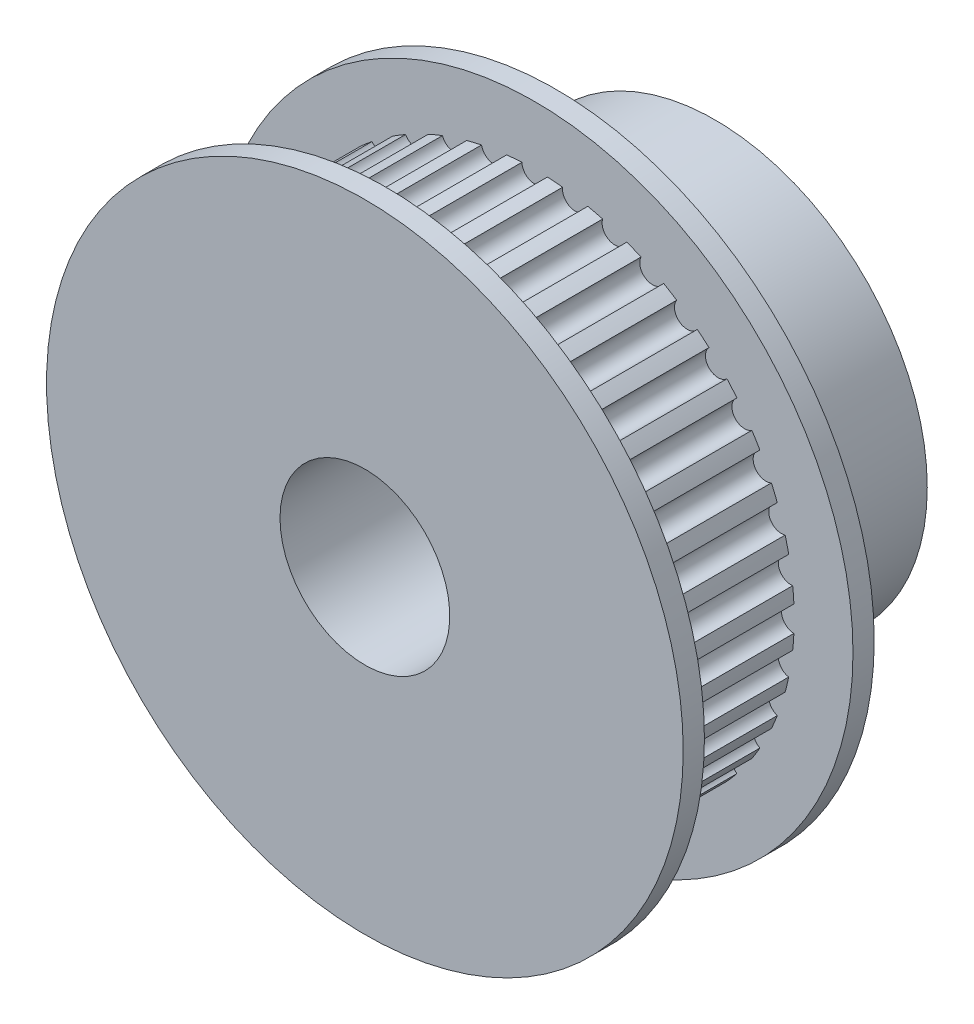
SolidWorks part; units mm, degrees
material "6061 合金"
ref_plane "前基準面" through (0, 0, 0) normal (0, 0, 1) x (1, 0, 0)
ref_plane "上基準面" through (0, 0, 0) normal (0, 1, 0) x (1, 0, 0)
ref_plane "右基準面" through (0, 0, 0) normal (1, 0, 0) x (0, 0, -1)
sketch "草圖1" plane through (0, 0, 0) normal (0, 0, 1) x (1, 0, 0)
  circle A0 centre (0, 0) radius 15
  dimension "D1" = 30
extrude "填料-伸長1" add sketch "草圖1" along normal mid plane 1
sketch "草圖2" plane through (0, 0, 0.5) normal (0, 0, 1) x (1, 0, 0)
  circle A0 centre (0, 0) radius 12.23
  dimension "D1" = 24.46
extrude "填料-伸長2" add sketch "草圖2" along normal blind 7
sketch "草圖8" plane through (0, 0, 0) normal (0, 0, -1) x (-1, 0, 0)
  circle A0 centre (0, 0) radius 10
  point P3 (0, 0)
  dimension "D1" = 20
extrude "填料-伸長4" add sketch "草圖8" along normal blind 8
sketch "草圖7" plane through (0, 0, 7.5) normal (0, 0, 1) x (1, 0, 0)
  line L0 (0, 0) -> (0, 12.23) construction
  arc A0 (-0.5998, 12.2153) -> (0.5998, 12.2153) centre (0, 12.23) ccw
  circle A1 centre (0, 0) radius 12.23 construction
  circle A2 centre (0, 0) radius 12.23 construction
  arc A3 (-0.5998, 12.2153) -> (0.5998, 12.2153) centre (0, 0) cw
  point P10 (0, 11.63)
  dimension "D1" = 0.6
extrude "除料-伸長3" cut sketch "草圖7" against normal up to surface (7 mm away) up to face at (12.23, 0, 0.5)
sketch "草圖3" plane through (0, 0, 7.5) normal (0, 0, 1) x (1, 0, 0)
  circle A0 centre (0, 0) radius 15
  circle A1 centre (0, 0) radius 15 construction
extrude "填料-伸長3" add sketch "草圖3" along normal blind 1
sketch "草圖6" plane through (0, 0, -0.5) normal (0, 0, -1) x (-1, 0, 0)
  circle A0 centre (0, 0) radius 4
  dimension "D1" = 8
extrude "除料-伸長2" cut sketch "草圖6" against normal through all both and the other way through all
pattern_circular "環狀複製排列2" count 40 over 360 about axis through (0, 0, 0) along (0, 0, 1) of "除料-伸長3"
